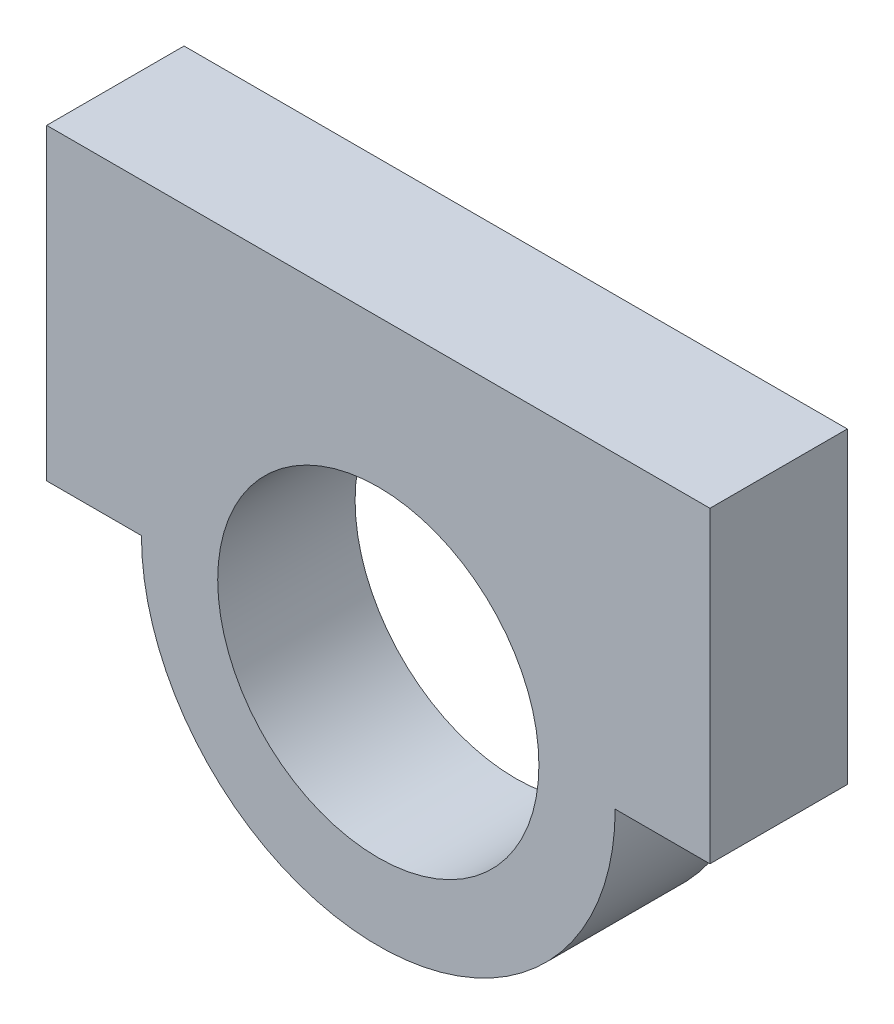
SolidWorks part; units mm, degrees
ref_plane "Спереди" through (0, 0, 0) normal (0, 0, 1) x (1, 0, 0)
ref_plane "Сверху" through (0, 0, 0) normal (0, 1, 0) x (1, 0, 0)
ref_plane "Справа" through (0, 0, 0) normal (1, 0, 0) x (0, 0, -1)
sketch "Эскиз1" plane through (0, 0, 0) normal (0, 0, 1) x (1, 0, 0)
  line L0 (-70, 65) -> (70, 65)
  line L1 (70, 65) -> (70, 0)
  line L2 (70, 0) -> (50, 0)
  line L4 (-50, 0) -> (-70, 0)
  line L5 (-70, 0) -> (-70, 65)
  circle A0 centre (0, 0) radius 33.9
  circle A1 centre (0, 0) radius 50
  dimension "D1" = 67.8
  dimension "D2" = 100
  dimension "D3" = 65
  dimension "D4" = 20
extrude "Бобышка-Вытянуть1" add sketch "Эскиз1" along normal blind 29 contours A1 A0 | A1 L2 L1 L0 L5 L4
